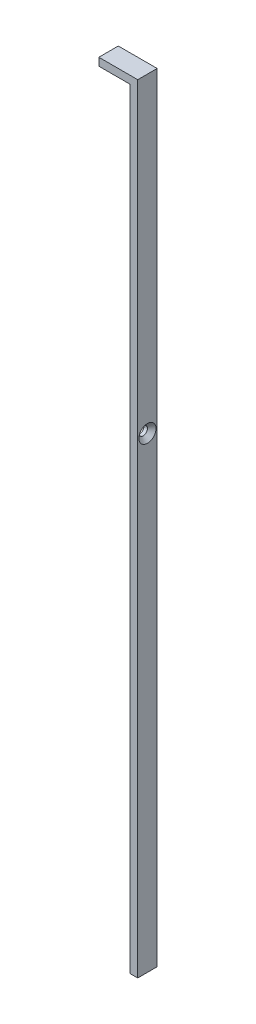
SolidWorks part; units mm, degrees
ref_plane "Front Plane" through (0, 0, 0) normal (0, 0, 1) x (1, 0, 0)
ref_plane "Top Plane" through (0, 0, 0) normal (0, 1, 0) x (1, 0, 0)
ref_plane "Right Plane" through (0, 0, 0) normal (1, 0, 0) x (0, 0, -1)
sketch "Sketch1" plane through (0, 0, 0) normal (0, 0, 1) x (1, 0, 0)
  line L0 (-8, 0) -> (0, 0)
  line L1 (0, 0) -> (0, -198)
  line L2 (0, -198) -> (2, -198)
  line L3 (2, -198) -> (2, 2)
  line L4 (2, 2) -> (-8, 2)
  line L5 (-8, 2) -> (-8, 0)
  dimension "D1" = 2
  dimension "D2" = 10
  dimension "D3" = 200
extrude "Boss-Extrude1" add sketch "Sketch1" along normal blind 5
sketch "Sketch2" plane through (2, 0, 0) normal (1, 0, 0) x (0, 0, -1)
  line L0 (-2.5, 2) -> (-2.5, -78) construction
  line L1 (-5, 2) -> (0, 2) construction
  point P5 (-2.5, -78)
  dimension "D1" = 80
hole_wizard "CSK for M2 Flat Head Machine Screw1" positions "3DSketch1" profile "Sketch3" countersink size "M2" standard "ANSI Metric" end condition up to next
sketch3d "3DSketch1"
  point P0 (2, -78, 2.5)
sketch "Sketch3" plane through (2, -78, 2.5) normal (0, 1, 0) x (0, 0, -1)
  line L0 (0, 0) -> (0, 2)
  line L1 (0, 2) -> (1.1, 2)
  line L2 (1.1, 2) -> (1.1, 1.1)
  line L3 (1.1, 1.1) -> (2.2, 0)
  line L5 (2.2, 0) -> (0, 0)
  line L6 (-1.1, 1.1) -> (-2.2, 0) construction
  line L11 (0, -6.35) -> (0, 107.95) construction
  dimension "Thru Hole Dia." = 2.2
  dimension "Thru Hole Depth" = 2
  dimension "Near C'Sink Dia." = 4.4
  dimension "Near C'Sink Angle" = 90
